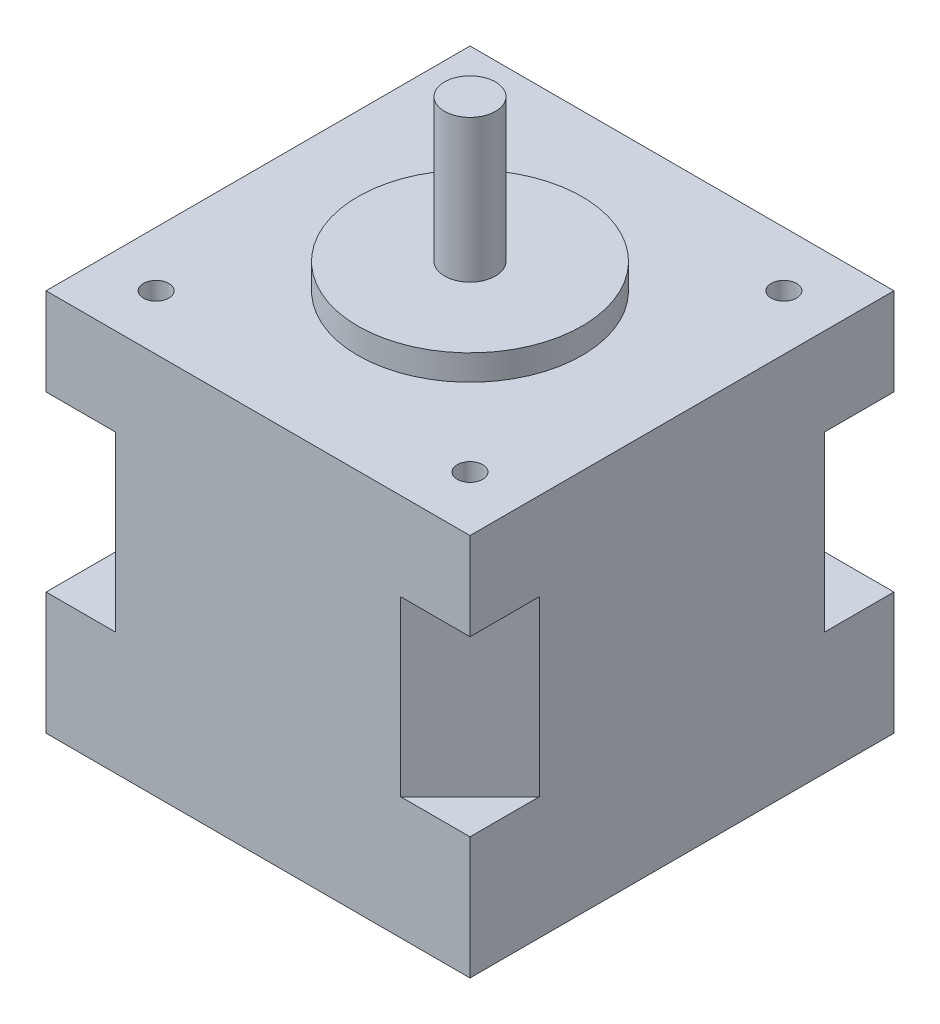
SolidWorks part; units mm, degrees
ref_plane "Front Plane" through (0, 0, 0) normal (0, 0, 1) x (1, 0, 0)
ref_plane "Top Plane" through (0, 0, 0) normal (0, 1, 0) x (1, 0, 0)
ref_plane "Right Plane" through (0, 0, 0) normal (1, 0, 0) x (0, 0, -1)
sketch "Sketch1" plane through (0, 0, 0) normal (0, 1, 0) x (1, 0, 0)
  line L1 (-20.8, 20.8) -> (20.8, 20.8)
  line L2 (-20.8, 20.8) -> (-20.8, -20.8)
  line L3 (-20.8, -20.8) -> (20.8, -20.8)
  line L4 (20.8, 20.8) -> (20.8, -20.8)
  line L5 (-20.8, 20.8) -> (20.8, -20.8) construction
  line L6 (-20.8, -20.8) -> (20.8, 20.8) construction
  point P0 (0, 0)
  dimension "D1" = 41.6
  dimension "D2" = 41.6
extrude "Boss-Extrude1" add sketch "Sketch1" along normal blind 37.6
sketch "Sketch2" plane through (0, 37.6, 0) normal (0, 1, 0) x (1, 0, 0)
  circle A0 centre (0, 0) radius 11
  dimension "D1" = 22
extrude "Boss-Extrude2" add sketch "Sketch2" along normal blind 2.5
sketch "Sketch3" plane through (0, 40.1, 0) normal (0, 1, 0) x (1, 0, 0)
  circle A0 centre (0, 0) radius 2.5
  dimension "D1" = 5
extrude "Boss-Extrude3" add sketch "Sketch3" along normal blind 14
sketch "Sketch4" plane through (0, 37.6, 0) normal (0, 1, 0) x (1, 0, 0)
  line L0 (20.8, 20.8) -> (-20.8, 20.8) construction
  line L1 (20.8, -20.8) -> (20.8, 20.8) construction
  circle A0 centre (15.4, 15.4) radius 1.25
  dimension "D1" = 2.5
  dimension "D2" = 5.4
  dimension "D3" = 5.4
extrude "Cut-Extrude1" cut sketch "Sketch4" against normal blind 8
mirror "Mirror1" about plane through (0, 0, 0) normal (1, 0, 0) of "Cut-Extrude1"
mirror "Mirror2" about plane through (0, 0, 0) normal (0, 0, 1) of "Mirror1", "Cut-Extrude1"
sketch "Sketch6" plane through (0, 0, 20.8) normal (0, 0, 1) x (1, 0, 0)
  line L0 (-20.8, 0) -> (-20.8, 12)
  line L1 (-20.8, 37.6) -> (-20.8, 0) construction
  line L2 (-20.8, 12) -> (20.8, 12)
  line L3 (20.8, 37.6) -> (20.8, 0) construction
  dimension "D1" = 12
sketch "Sketch7" plane through (-20.8, 0, 0) normal (-1, 0, 0) x (0, 0, 1)
  line L0 (20.8, 12) -> (-20.8, 12)
  line L1 (-20.8, 37.6) -> (-20.8, 0) construction
ref_plane "Plane1" through (0, 12, 0) normal (0, 1, 0) x (1, 0, 0)
sketch "Sketch9" plane through (0, 12, 0) normal (0, 1, 0) x (1, 0, 0)
  line L0 (0, 20.8) -> (14, 20.8)
  line L1 (20.8, 20.8) -> (-20.8, 20.8) construction
  line L2 (20.8, 0) -> (20.8, 14)
  line L3 (20.8, -20.8) -> (20.8, 20.8) construction
  line L4 (20.8, 14) -> (14, 20.8)
  line L5 (14, 20.8) -> (20.8, 20.8)
  line L6 (20.8, 20.8) -> (20.8, 14)
  dimension "D1" = 14
  dimension "D2" = 14
extrude "Cut-Extrude2" cut sketch "Sketch9" along normal blind 17 contours L4 L5 L6
mirror "Mirror3" about plane through (0, 0, 0) normal (0, 0, 1) of "Cut-Extrude2"
mirror "Mirror4" about plane through (0, 0, 0) normal (1, 0, 0) of "Mirror3", "Cut-Extrude2"
sketch "Sketch10" plane through (0, 0, 0) normal (0, -1, 0) x (1, 0, 0)
  circle A0 centre (0, 0) radius 4.3
  dimension "D1" = 8.6
extrude "Cut-Extrude3" cut sketch "Sketch10" against normal blind 5.7
